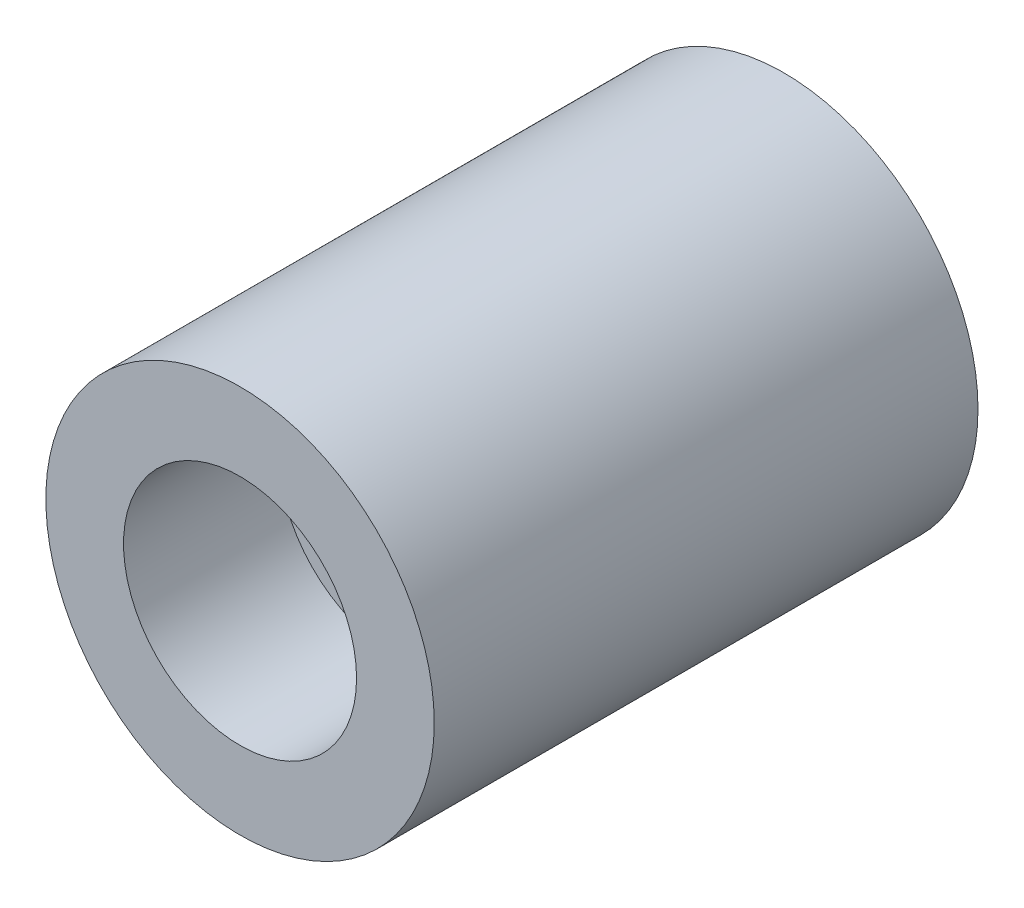
SolidWorks part; units mm, degrees
ref_plane "Front Plane" through (0, 0, 0) normal (0, 0, 1) x (1, 0, 0)
ref_plane "Top Plane" through (0, 0, 0) normal (0, 1, 0) x (1, 0, 0)
ref_plane "Right Plane" through (0, 0, 0) normal (1, 0, 0) x (0, 0, -1)
sketch "Sketch1" plane through (0, 0, 0) normal (0, 0, 1) x (1, 0, 0)
  circle A0 centre (0, 0) radius 50
  dimension "D1" = 100
extrude "Boss-Extrude1" add sketch "Sketch1" along normal blind 140
sketch "Sketch2" plane through (0, 0, 140) normal (0, 0, 1) x (1, 0, 0)
  circle A0 centre (0, 0) radius 30
  dimension "D1" = 60
extrude "Cut-Extrude1" cut sketch "Sketch2" against normal blind 40
sketch "Sketch3" plane through (0, 0, 140) normal (0, 0, 1) x (1, 0, 0)
  circle A0 centre (0, 0) radius 10
  dimension "D1" = 20
extrude "Cut-Extrude2" cut sketch "Sketch3" against normal blind 120
